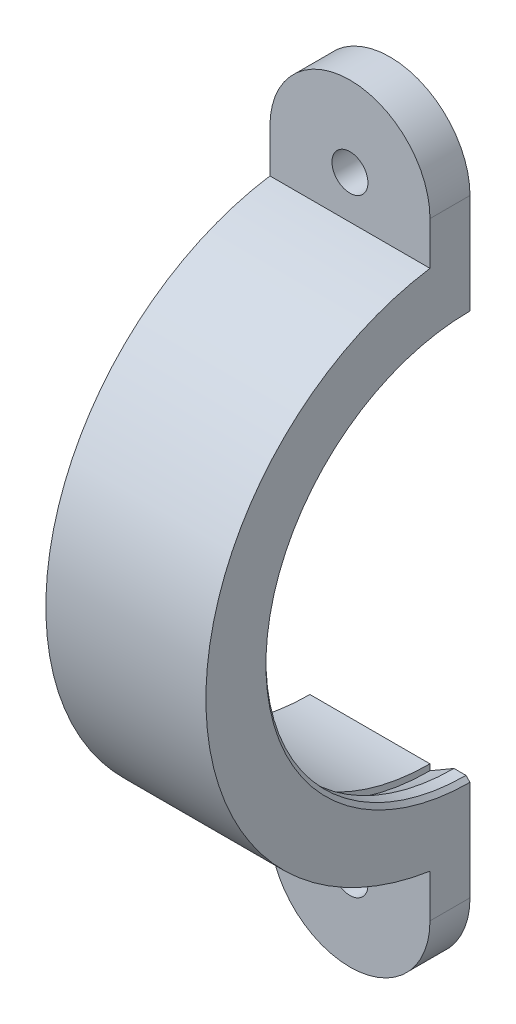
SolidWorks part; units mm, degrees
ref_plane "Front Plane" through (0, 0, 0) normal (0, 0, 1) x (1, 0, 0)
ref_plane "Top Plane" through (0, 0, 0) normal (0, 1, 0) x (1, 0, 0)
ref_plane "Right Plane" through (0, 0, 0) normal (1, 0, 0) x (0, 0, -1)
sketch "Sketch1" plane through (0, 0, 0) normal (0, 0, 1) x (1, 0, 0)
  line L0 (0, 33) -> (20, 33)
  line L1 (18, 25) -> (20, 25)
  line L2 (20, 33) -> (20, 25)
  line L3 (0, 0) -> (50.1034, 0)
  line L4 (0, 33) -> (0, 26)
  line L5 (0, 26) -> (15, 26)
  line L6 (15, 26) -> (15, 26.75)
  line L7 (15, 26.75) -> (18, 25)
  dimension "D1" = 15
  dimension "D2" = 2
  dimension "D3" = 0.75
  dimension "D4" = 3
  dimension "D5" = 1
  dimension "D6" = 7
  dimension "D7" = 26
  dimension "D8" = 0
revolve "Revolve1" add sketch "Sketch1" angle 180 about L3
sketch3d "3DSketch1" plane through (0, 0, 0) normal (0, 0, 1) x (1, 0, 0)
sketch "Sketch9" plane through (0, 0, 0) normal (0, 0, -1) x (-1, 0, 0)
  line L0 (-20, 33) -> (-20, 25) construction
  line L1 (-20, 29) -> (0, 29)
  line L2 (-20, 29) -> (-20, 38)
  line L4 (0, 29) -> (0, 38)
  arc A0 (0, 38) -> (-20, 38) centre (-10, 38) ccw
  dimension "D1" = 5
extrude "Boss-Extrude3" add sketch "Sketch9" against normal blind 5
sketch3d "3DSketch2" plane through (0, 0, 0) normal (0, 0, 1) x (1, 0, 0)
  dimension "D1" = 90
sketch "Sketch11" plane through (0, 0, 0) normal (0, 0, -1) x (-1, 0, 0)
  line L0 (-20, -33) -> (-20, -25) construction
  line L1 (-20, -29) -> (0, -29)
  line L2 (-20, -29) -> (-20, -38)
  line L4 (0, -29) -> (0, -38)
  arc A0 (0, -38) -> (-20, -38) centre (-10, -38) cw
  dimension "D1" = 5
extrude "Boss-Extrude4" add sketch "Sketch11" against normal blind 5
sketch "Sketch17" plane through (0, 0, 0) normal (0, 0, -1) x (-1, 0, 0)
  circle A0 centre (-10, 38) radius 2.2479
  circle A1 centre (-10, -38) radius 2.2479
  dimension "D1" = 4.4958
  dimension "D2" = 4.4958
extrude "Cut-Extrude1" cut sketch "Sketch17" against normal through all
chamfer "Chamfer1" distance 0.5 angle 45 1 edges at (20, 0, 25)
